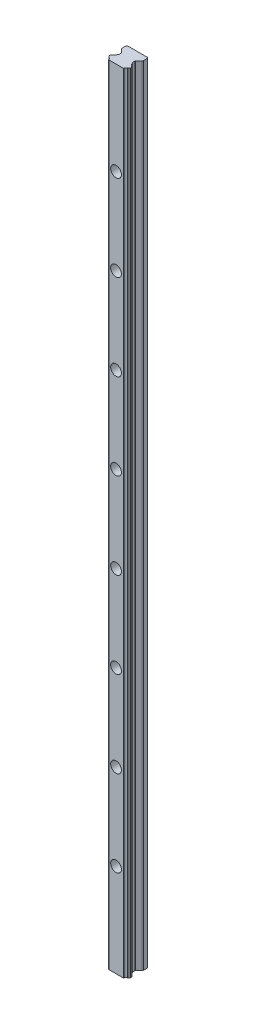
SolidWorks part; units mm, degrees
ref_plane "Ebene vorne" through (0, 0, 0) normal (0, 0, 1) x (1, 0, 0)
ref_plane "Ebene oben" through (0, 0, 0) normal (0, 1, 0) x (1, 0, 0)
ref_plane "Ebene rechts" through (0, 0, 0) normal (1, 0, 0) x (0, 0, -1)
other "Schienenlänge"
sketch "Skizze20" plane through (0, 0, 0) normal (0, 1, 0) x (-1, 0, 0)
  line L48 (5.0861, 14.9629) -> (5.049, 15)
  line L49 (5.049, 15) -> (-5.049, 15)
  line L50 (-5.049, 15) -> (-5.0861, 14.9629)
  line L51 (-6.775, 13.2021) -> (-6.8053, 13.0612)
  line L52 (-7.0777, 12.7633) -> (-7.2187, 12.7195)
  line L53 (-7.5, 12.3375) -> (-7.5, 11.5815)
  line L54 (-7.2357, 11.2052) -> (-7.0606, 11.1421)
  line L55 (-6.8062, 10.8541) -> (-6.7743, 10.7128)
  line L56 (-5.0816, 8.5926) -> (-4.8872, 8.3982)
  line L57 (-4.77, 8.1153) -> (-4.77, 6.5533)
  line L58 (-4.8872, 6.2704) -> (-7.2071, 3.9505)
  line L59 (-7.5, 3.2434) -> (-7.5, 0.7)
  line L60 (-7.5, 0.7) -> (-6.8, 0)
  line L61 (-6.8, 0) -> (6.8, 0)
  line L62 (6.8, 0) -> (7.5, 0.7)
  line L63 (7.5, 0.7) -> (7.5, 3.2434)
  line L64 (7.2071, 3.9505) -> (4.8872, 6.2704)
  line L65 (4.77, 6.5533) -> (4.77, 8.1153)
  line L66 (4.8872, 8.3982) -> (5.0816, 8.5926)
  line L67 (6.7743, 10.7128) -> (6.8062, 10.8541)
  line L68 (7.0606, 11.1421) -> (7.2357, 11.2052)
  line L69 (7.5, 11.5815) -> (7.5, 12.3375)
  line L70 (7.2187, 12.7195) -> (7.0777, 12.7633)
  line L71 (6.8053, 13.0612) -> (6.775, 13.2021)
  arc A52 (5.274, 14.8234) -> (6.4784, 13.5067) centre (6.8562, 15.0614) ccw
  arc A53 (5.274, 14.8234) -> (5.0861, 14.9629) centre (4.9521, 14.586) ccw
  arc A54 (-5.0861, 14.9629) -> (-5.274, 14.8234) centre (-4.9521, 14.586) ccw
  arc A55 (-6.4784, 13.5067) -> (-5.274, 14.8234) centre (-6.8562, 15.0614) ccw
  arc A56 (-6.4784, 13.5067) -> (-6.775, 13.2021) centre (-6.384, 13.118) ccw
  arc A57 (-7.0777, 12.7633) -> (-6.8053, 13.0612) centre (-7.1964, 13.1453) ccw
  arc A58 (-7.2187, 12.7195) -> (-7.5, 12.3375) centre (-7.1, 12.3375) ccw
  arc A59 (-7.5, 11.5815) -> (-7.2357, 11.2052) centre (-7.1, 11.5815) ccw
  arc A60 (-6.8062, 10.8541) -> (-7.0606, 11.1421) centre (-7.1964, 10.7658) ccw
  arc A61 (-6.7743, 10.7128) -> (-6.4785, 10.4123) centre (-6.3841, 10.801) ccw
  arc A62 (-5.2706, 9.0718) -> (-6.4785, 10.4123) centre (-6.8562, 8.8576) ccw
  arc A63 (-5.2706, 9.0718) -> (-5.0816, 8.5926) centre (-4.8914, 8.9445) ccw
  arc A64 (-4.77, 8.1153) -> (-4.8872, 8.3982) centre (-5.17, 8.1153) ccw
  arc A65 (-4.8872, 6.2704) -> (-4.77, 6.5533) centre (-5.17, 6.5533) ccw
  arc A66 (-7.2071, 3.9505) -> (-7.5, 3.2434) centre (-6.5, 3.2434) ccw
  arc A67 (7.5, 3.2434) -> (7.2071, 3.9505) centre (6.5, 3.2434) ccw
  arc A68 (4.77, 6.5533) -> (4.8872, 6.2704) centre (5.17, 6.5533) ccw
  arc A69 (4.8872, 8.3982) -> (4.77, 8.1153) centre (5.17, 8.1153) ccw
  arc A70 (5.0816, 8.5926) -> (5.2706, 9.0718) centre (4.8914, 8.9445) ccw
  arc A71 (6.4785, 10.4123) -> (5.2706, 9.0718) centre (6.8562, 8.8576) ccw
  arc A72 (6.4785, 10.4123) -> (6.7743, 10.7128) centre (6.3841, 10.801) ccw
  arc A73 (7.0606, 11.1421) -> (6.8062, 10.8541) centre (7.1964, 10.7658) ccw
  arc A74 (7.2357, 11.2052) -> (7.5, 11.5815) centre (7.1, 11.5815) ccw
  arc A75 (7.5, 12.3375) -> (7.2187, 12.7195) centre (7.1, 12.3375) ccw
  arc A76 (6.8053, 13.0612) -> (7.0777, 12.7633) centre (7.1964, 13.1453) ccw
  arc A77 (6.775, 13.2021) -> (6.4784, 13.5067) centre (6.384, 13.118) ccw
  dimension "D1" = 4.9521
  dimension "D2" = 5.274
  dimension "D3" = 4.9521
  dimension "D4" = 5.274
  dimension "D5" = 0.7
  dimension "D6" = 14.586
extrude "Aufsatz-Linear austragen2" add sketch "Skizze20" along normal mid plane 550 contours L49 L50 A54 A55 A56 L51 A57 L52 A58 L53 A59 L54 A60 L55 A61 A62 A63 L56 A64 L57 A65 L58 A66 L59 L60 L61 L62 L63 A67 L64 A68 L65 A69 L66 A70 A71 A72 L67 A73 L68 A74 L69 A75 L70 A76 L71 A77 A52 A53 L48
hole_wizard "Stirnsenkung für M4 Zylinderschraube mit Innensechskant1" positions "Skizze19" profile "Skizze18" counterbore size "M4" standard "DIN" end condition through all
sketch "Skizze19" plane through (0, 0, 15) normal (0, 0, -1) x (-1, 0, 0)
  line L2 (5.049, 0) -> (-5.049, 0) construction
  line L3 (5.049, 275) -> (5.049, -275) construction
  line L4 (-5.049, 275) -> (-5.049, -275) construction
  point P0 (0, -30)
  point P65 (0, 0)
  dimension "D1" = 30
sketch "Skizze18" plane through (0, -30, 15) normal (1, 0, 0) x (0, -1, 0)
  line L0 (0, 0) -> (0, 15)
  line L1 (0, 15) -> (2.25, 15)
  line L3 (2.25, 15) -> (2.25, 5.3)
  line L4 (2.25, 5.3) -> (3.75, 5.3)
  line L5 (3.75, 5.3) -> (3.75, 0)
  line L7 (3.75, 0) -> (0, 0)
  line L11 (0, -6.35) -> (0, 107.95) construction
  dimension "Bohrerdurchmesser" = 4.5
  dimension "Bohrungstiefe" = 15
  dimension "Senkdurchmesser2" = 7.5
  dimension "Senktiefe2" = 5.3
pattern_linear "Lineares Muster1" count 5 spacing 60 along (0, 1, 0) count 4 spacing 60 along (0, -1, 0) of "Stirnsenkung für M4 Zylinderschraube mit Innensechskant1"
